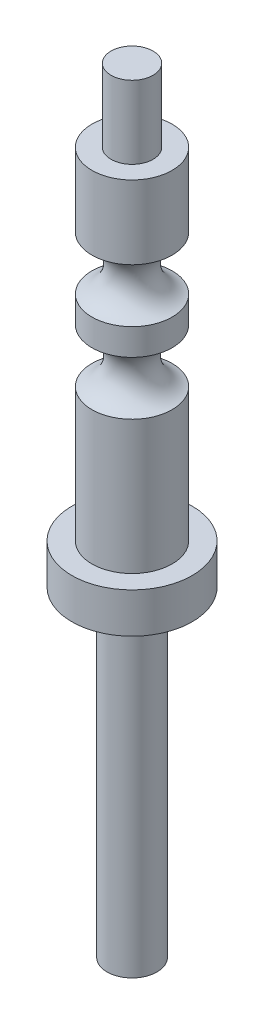
SolidWorks part; units mm, degrees
ref_plane "Front Plane" through (0, 0, 0) normal (0, 0, 1) x (1, 0, 0)
ref_plane "Top Plane" through (0, 0, 0) normal (0, 1, 0) x (1, 0, 0)
ref_plane "Right Plane" through (0, 0, 0) normal (1, 0, 0) x (0, 0, -1)
sketch "Sketch1" plane through (0, 0, 0) normal (0, 0, 1) x (1, 0, 0)
  line L0 (0, 0) -> (0, 79.052) construction
  line L1 (0, 0) -> (1.9812, 0)
  line L2 (1.9812, 0) -> (1.9812, 25.4)
  line L3 (1.9812, 25.4) -> (3.175, 25.4)
  line L4 (3.175, 25.4) -> (3.175, 55.5625)
  line L5 (3.175, 55.5625) -> (1.6637, 55.5625)
  line L6 (1.6637, 55.5625) -> (1.6637, 61.3283)
  line L7 (1.6637, 61.3283) -> (0, 61.3283)
  line L11 (0, 61.3283) -> (0, 0)
  dimension "D1" = 25.4
  dimension "D2" = 30.1625
  dimension "D3" = 5.7658
  dimension "D8" = 3.3274
  dimension "D9" = 6.35
  dimension "D10" = 3.9624
revolve "Revolve1" add sketch "Sketch1" angle 360 about L0
sketch "Sketch2" plane through (0, 25.4, 0) normal (0, -1, 0) x (1, 0, 0)
  circle A0 centre (0, 0) radius 4.7625
  dimension "D1" = 9.525
extrude "Boss-Extrude1" add sketch "Sketch2" against normal blind 3.175
sketch "Sketch3" plane through (0, 28.575, 0) normal (0, 1, 0) x (1, 0, 0)
  circle A0 centre (0, 0) radius 5.5626
  circle A1 centre (0, 0) radius 3.175
  dimension "D1" = 6.35
  dimension "D2" = 11.1252
extrude "Boss-Extrude2- Rubber Post Sleeve" [suppressed] add sketch "Sketch3" along normal blind 25.4
sketch "Sketch4" plane through (0, 0, 0) normal (1, 0, 0) x (0, 0, -1)
  line L0 (3.175, 28.575) -> (3.175, 55.5625) construction
  line L1 (3.175, 39.1541) -> (3.175, 43.3959)
  line L2 (0, 0) -> (0, 86.6005) construction
  line L3 (3.175, 39.1541) -> (5.9663, 39.1541) construction
  line L4 (3.175, 43.3959) -> (5.9663, 43.3959) construction
  line L6 (-4.7625, 25.4) -> (4.7625, 25.4) construction
  arc A0 (3.175, 43.3959) -> (3.175, 39.1541) centre (3.798, 41.275) ccw
  dimension "D1" = 1.5875
  dimension "D2" = 15.875
  dimension "D3" = 4.2418
revolve "Cut-Revolve1" cut sketch "Sketch4" angle 360 about L2
pattern_linear "LPattern1" count 2 spacing 6.35 along (0, 1, 0) of "Cut-Revolve1"
ref_plane "Plane1" through (0, 41.275, 0) normal (0, -1, 0) x (-1, 0, 0)
sketch "Sketch5" plane through (0, 41.275, 0) normal (0, -1, 0) x (-1, 0, 0)
  circle A0 centre (0, 0) radius 4.1275 construction
  dimension "D1" = 8.255
